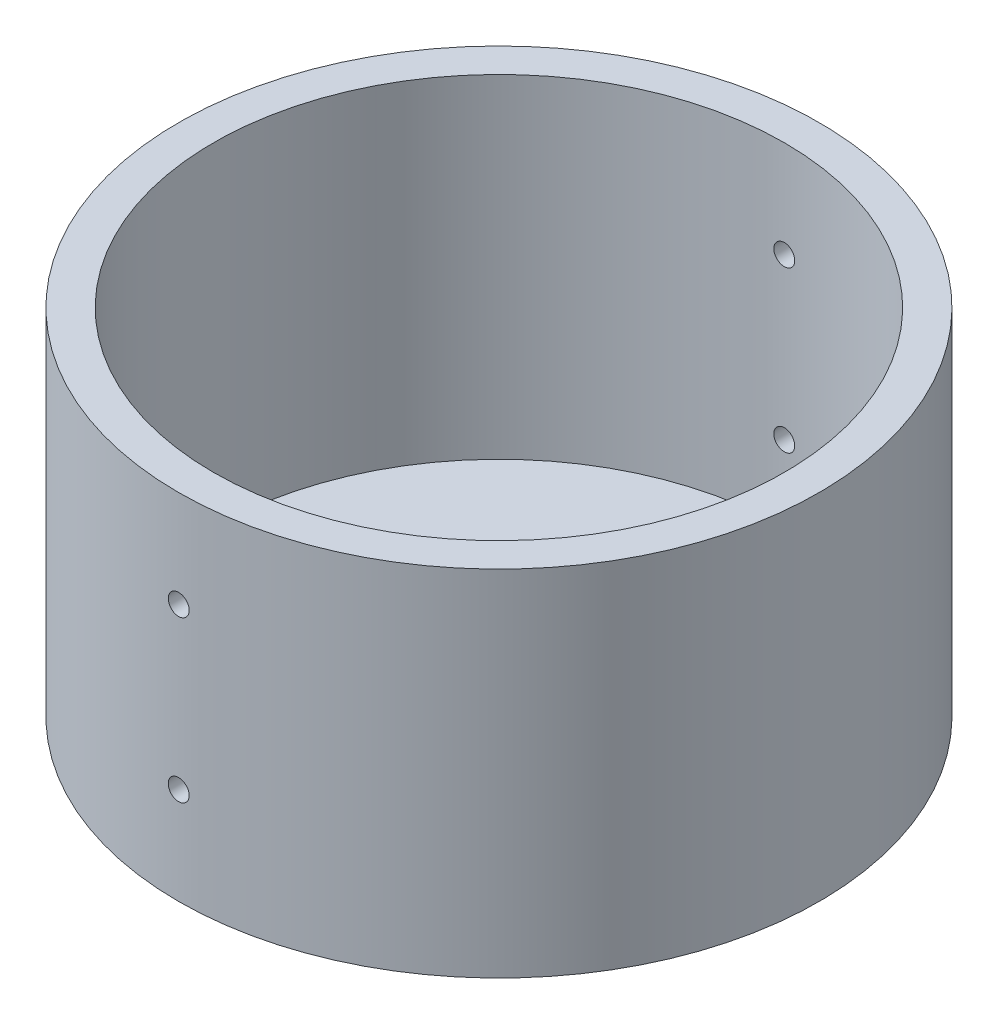
SolidWorks part; units mm, degrees
ref_plane "Front Plane" through (0, 0, 0) normal (0, 0, 1) x (1, 0, 0)
ref_plane "Top Plane" through (0, 0, 0) normal (0, 1, 0) x (1, 0, 0)
ref_plane "Right Plane" through (0, 0, 0) normal (1, 0, 0) x (0, 0, -1)
sketch "Sketch1" plane through (0, 0, 0) normal (0, 1, 0) x (1, 0, 0)
  circle A0 centre (0, 0) radius 45.95
  dimension "D1" = 91.9
extrude "Boss-Extrude1" add sketch "Sketch1" along normal blind 3
sketch "Sketch2" plane through (0, 3, 0) normal (0, 1, 0) x (1, 0, 0)
  circle A0 centre (0, 0) radius 45.95
  circle A1 centre (0, 0) radius 40.95
  dimension "D1" = 5
extrude "Boss-Extrude2" add sketch "Sketch2" along normal blind 22.4
sketch "Sketch3" plane through (0, 0, 0) normal (0, -1, 0) x (1, 0, 0)
  circle A0 centre (0, 0) radius 45.95
  circle A1 centre (0, 0) radius 42.95
  dimension "D1" = 3
sketch "Sketch6" plane through (0, 0, 0) normal (0, -1, 0) x (-1, 0, 0)
  line L0 (0, 0) -> (9.5, 0) construction
  circle A0 centre (0, 0) radius 9.5
  dimension "D1" = 19
sketch "Sketch11" plane through (0, 0, 0) normal (0, 0, 1) x (1, 0, 0)
  line L0 (0, 0) -> (0, 13.9) construction
  line L1 (-4.444, 0) -> (5.3042, 0) construction
  line L2 (-9.5, 0) -> (9.5, 0) construction
  line L4 (45.95, 25.4) -> (-45.95, 25.4) construction
  circle A0 centre (0, 13.9) radius 1.5
  circle A1 centre (0, -13.9) radius 1.5
  dimension "D2" = 3
  dimension "D3" = 11.5
  dimension "D1" = 13.9
extrude "Cut-Extrude1" cut sketch "Sketch11" against normal through all and the other way through all
sketch "Sketch12" plane through (0, 25.4, 0) normal (0, 1, 0) x (1, 0, 0)
  circle A0 centre (0, 0) radius 45.95
  circle A1 centre (0, 0) radius 40.95
extrude "Boss-Extrude3" add sketch "Sketch12" along normal blind 25.4
sketch "Sketch14" plane through (0, 0, 0) normal (0, 0, 1) x (1, 0, 0)
  line L0 (0, 13.9) -> (0, 36.9) construction
  circle A0 centre (0, 36.9) radius 1.5
  dimension "D2" = 3
  dimension "D1" = 23
extrude "Cut-Extrude2" cut sketch "Sketch14" against normal through all and the other way through all
sketch "Sketch15" plane through (0, 3, 0) normal (0, 1, 0) x (1, 0, 0)
  circle A0 centre (0, 0) radius 4
  dimension "D1" = 8
sketch "Sketch17" plane through (0, 3, 0) normal (0, 1, 0) x (1, 0, 0)
  circle A0 centre (0, 9.5) radius 1.5
  circle A1 centre (0, 0) radius 9.5 construction
  circle A2 centre (8.2272, 4.75) radius 1.5
  circle A3 centre (8.2272, -4.75) radius 1.5
  circle A4 centre (0, -9.5) radius 1.5
  circle A5 centre (-8.2272, -4.75) radius 1.5
  circle A6 centre (-8.2272, 4.75) radius 1.5
  point P16 (0, 0)
  dimension "D1" = 3
  dimension "D2" = 6
extrude "Cut-Extrude4" cut sketch "Sketch17" against normal blind 10
extrude "Cut-Extrude6" cut sketch "Sketch15" against normal blind 10
